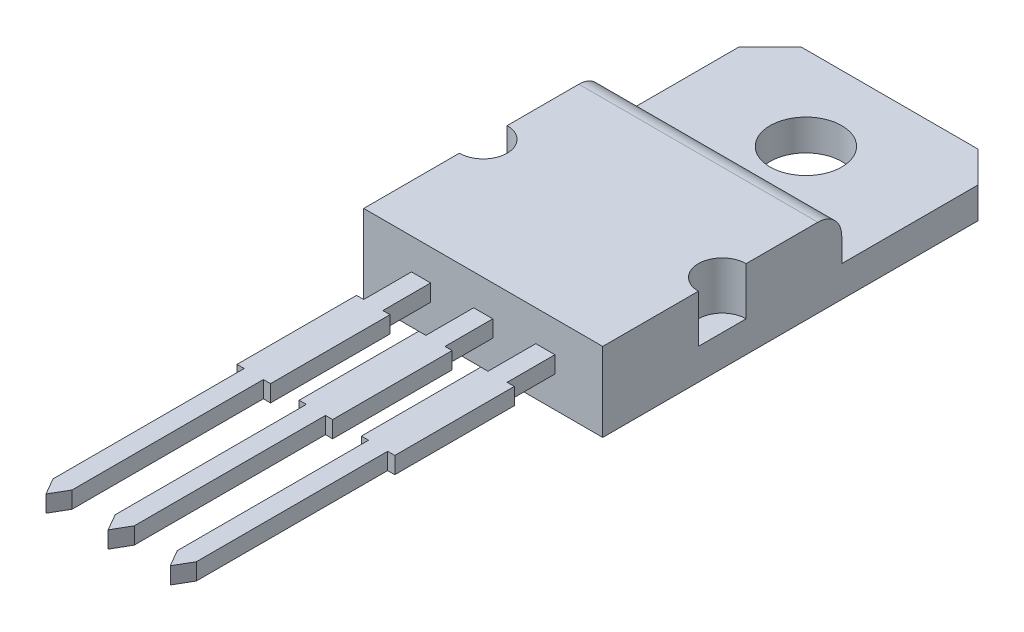
SolidWorks part; units mm, degrees
ref_plane "Front Plane" through (0, 0, 0) normal (0, 0, 1) x (1, 0, 0)
ref_plane "Top Plane" through (0, 0, 0) normal (0, 1, 0) x (1, 0, 0)
ref_plane "Right Plane" through (0, 0, 0) normal (1, 0, 0) x (0, 0, -1)
sketch "Sketch1" plane through (0, 0, 0) normal (0, 1, 0) x (1, 0, 0)
  line L0 (0.4, 18.9846) -> (0.4, -5.9522) construction
  line L1 (-0.9, 18.9846) -> (-0.9, -7.1778) construction
  line L2 (0, 0) -> (0, 8)
  line L3 (0, 15) -> (0.8, 15)
  line L4 (0.8, 0) -> (0.8, 8)
  line L5 (0, 0) -> (0.4, -0.6928)
  line L6 (0.4, -0.6928) -> (0.8, 0)
  line L7 (0, 13) -> (0, 15)
  line L8 (-0.3, 13) -> (0, 13)
  line L9 (-0.3, 13) -> (-0.3, 8)
  line L10 (-0.3, 8) -> (0, 8)
  line L11 (1.1, 13) -> (1.1, 8)
  line L12 (0.8, 8) -> (1.1, 8)
  line L13 (0.8, 13) -> (0.8, 15)
  line L14 (0.8, 13) -> (1.1, 13)
  line L15 (-1.8, 15) -> (-2.6, 15)
  line L16 (-2.6, 13) -> (-2.6, 15)
  line L17 (-1.8, 13) -> (-1.8, 15)
  line L18 (-1.5, 13) -> (-1.8, 13)
  line L19 (-2.6, 13) -> (-2.9, 13)
  line L20 (-2.9, 13) -> (-2.9, 8)
  line L21 (-1.5, 13) -> (-1.5, 8)
  line L22 (-2.6, 8) -> (-2.9, 8)
  line L23 (-1.5, 8) -> (-1.8, 8)
  line L24 (-2.6, 0) -> (-2.6, 8)
  line L25 (-2.2, -0.6928) -> (-2.6, 0)
  line L26 (-1.8, 0) -> (-2.2, -0.6928)
  line L27 (-1.8, 0) -> (-1.8, 8)
  line L28 (2.08, 10.5) -> (-12.6034, 10.5) construction
  line L29 (-5.5, 13) -> (-5.5, 8)
  line L30 (-5.2, 13) -> (-5.5, 13)
  line L31 (-5.2, 13) -> (-5.2, 15)
  line L32 (-4.4, 15) -> (-5.2, 15)
  line L33 (-4.4, 13) -> (-4.4, 15)
  line L34 (-4.1, 13) -> (-4.4, 13)
  line L35 (-4.1, 13) -> (-4.1, 8)
  line L36 (-4.1, 8) -> (-4.4, 8)
  line L37 (-5.2, 8) -> (-5.5, 8)
  line L38 (-5.2, 0) -> (-5.2, 8)
  line L39 (-4.4, 0) -> (-4.4, 8)
  line L40 (-4.8, -0.6928) -> (-5.2, 0)
  line L41 (-4.4, 0) -> (-4.8, -0.6928)
  point P12 (0.4, 15)
  dimension "D1" = 15
  dimension "D2" = 0.8
  dimension "D3" = 0.8
  dimension "D4" = 2
  dimension "D5" = 1.4
  dimension "D6" = 5
  dimension "D7" = 60
  dimension "D8" = 0.6
  dimension "D9" = 0.6
  dimension "D11" = 2
  dimension "D10" = 2
extrude "Boss-Extrude1" add sketch "Sketch1" along normal blind 0.7
sketch "Sketch2" plane through (0, 0, 0) normal (0, 1, 0) x (1, 0, 0)
  line L0 (-2.2, -2.6788) -> (-2.2, 23.4889) construction
  line L1 (-7.2, 15) -> (2.8, 15)
  line L2 (-7.2, 15) -> (-7.2, 25)
  line L3 (-7.2, 25) -> (2.8, 25)
  line L4 (2.8, 15) -> (2.8, 25)
  dimension "D1" = 10
  dimension "D2" = 10
extrude "Boss-Extrude2" add sketch "Sketch2" along normal blind 2
fillet "Fillet1" radius 1 1 edges at (-2.2, 2, -25)
sketch "Sketch3" plane through (0, 2, 0) normal (0, 1, 0) x (1, 0, 0)
  line L0 (-7.2, 20) -> (2.8, 20) construction
  line L4 (-7.2, 24) -> (-7.2, 15) construction
  line L5 (2.8, 15) -> (2.8, 24) construction
  line L6 (-7.2, 15) -> (2.8, 15) construction
  circle A0 centre (-7.2, 20) radius 1
  circle A1 centre (2.8, 20) radius 1
  dimension "D2" = 2
  dimension "D1" = 5
extrude "Cut-Extrude1" cut sketch "Sketch3" against normal blind 2
sketch "Sketch4" plane through (0, 0, 0) normal (0, -1, 0) x (1, 0, 0)
  line L0 (-7.2, -30.7) -> (-5.9, -32)
  line L1 (-7.2, -15) -> (2.8, -15)
  line L2 (-7.2, -15) -> (-7.2, -30.7)
  line L3 (-5.9, -32) -> (1.5, -32)
  line L4 (2.8, -15) -> (2.8, -30.7)
  line L5 (1.5, -32) -> (2.8, -30.7)
  point P1 (2.8, -32)
  point P2 (-7.2, -32)
  dimension "D1" = 17
  dimension "D2" = 7
extrude "Boss-Extrude3" add sketch "Sketch4" along normal blind 1.3
sketch "Sketch5" plane through (0, 0, 0) normal (0, 1, 0) x (1, 0, 0)
  line L0 (-2.2, 34.5942) -> (-2.2, 22.4058) construction
  line L2 (-5.9, 32) -> (1.5, 32) construction
  circle A0 centre (-2.2, 28.5) radius 1.5
  dimension "D1" = 3
  dimension "D2" = 3.5
extrude "Cut-Extrude2" cut sketch "Sketch5" against normal through all
